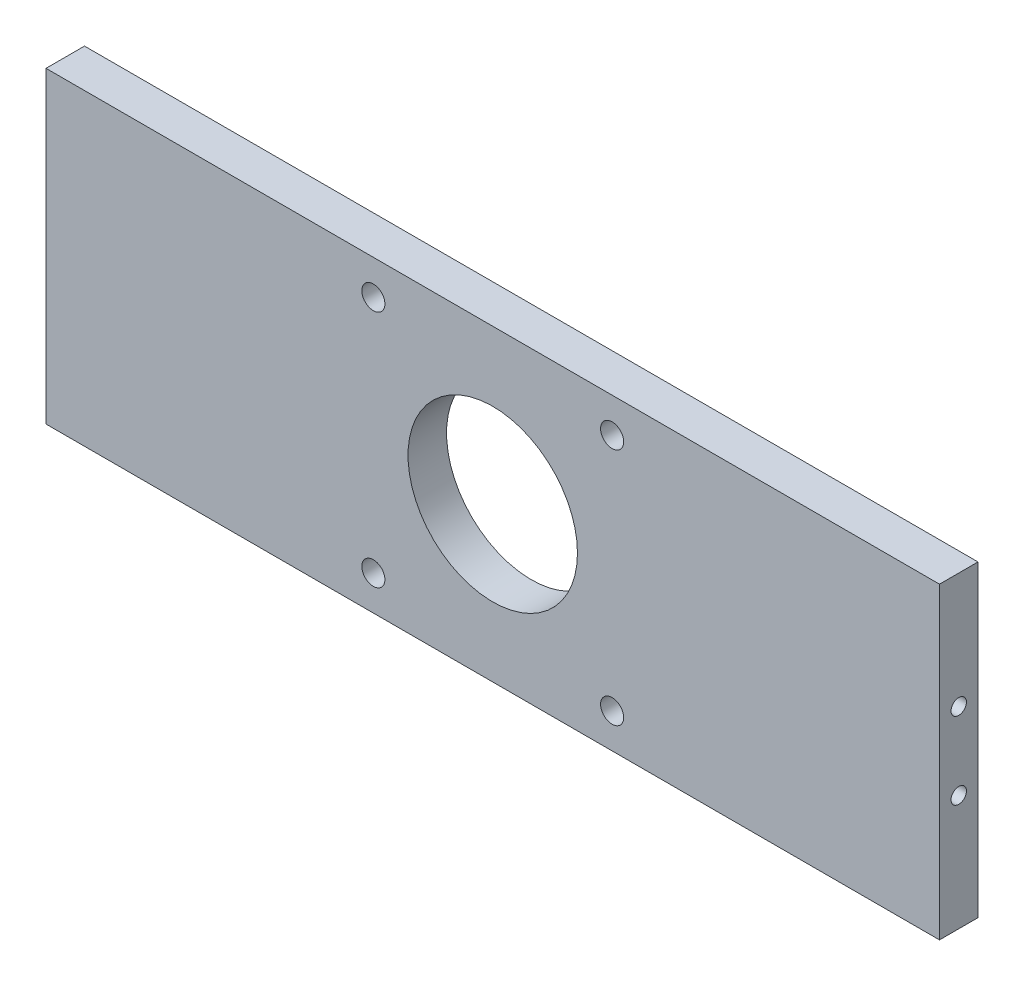
SolidWorks part; units mm, degrees
ref_plane "Front Plane" through (0, 0, 0) normal (0, 0, 1) x (1, 0, 0)
ref_plane "Top Plane" through (0, 0, 0) normal (0, 1, 0) x (1, 0, 0)
ref_plane "Right Plane" through (0, 0, 0) normal (1, 0, 0) x (0, 0, -1)
sketch "Sketch1" plane through (0, 0, 0) normal (0, 0, 1) x (1, 0, 0)
  line L1 (-58, 20) -> (58, 20)
  line L2 (-58, 20) -> (-58, -20)
  line L3 (-58, -20) -> (58, -20)
  line L4 (58, 20) -> (58, -20)
  line L5 (-58, 20) -> (58, -20) construction
  line L6 (-58, -20) -> (58, 20) construction
  line L7 (-15.5, 15.5) -> (15.5, 15.5)
  line L8 (-15.5, 15.5) -> (-15.5, -15.5)
  line L9 (-15.5, -15.5) -> (15.5, -15.5)
  line L10 (15.5, 15.5) -> (15.5, -15.5)
  line L11 (-15.5, 15.5) -> (15.5, -15.5) construction
  line L12 (-15.5, -15.5) -> (15.5, 15.5) construction
  circle A0 centre (0, 0) radius 11
  circle A1 centre (-15.5, 15.5) radius 1.5
  circle A2 centre (-15.5, -15.5) radius 1.5
  circle A3 centre (15.5, -15.5) radius 1.5
  circle A4 centre (15.5, 15.5) radius 1.5
  point P0 (0, 0)
  dimension "D3" = 22
  dimension "D6" = 3
  dimension "D7" = 3
  dimension "D8" = 3
  dimension "D9" = 3
  dimension "D1" = 40
  dimension "D2" = 116
  dimension "D4" = 31
  dimension "D5" = 31
extrude "Boss-Extrude2" add sketch "Sketch1" along normal blind 5 contours L4 L1 L2 L3 A4 L10 A3 L9 A2 L8 A1 L7 | A4 L7 A1 L8 A2 L9 A3 L10 A0
ref_plane "Plane1" through (58, 0, 0) normal (1, 0, 0) x (0, 0, -1)
sketch "Sketch4" plane through (58, 0, 0) normal (1, 0, 0) x (0, 0, -1)
  line L0 (-5, 0) -> (0, 0)
  line L1 (-5, 20) -> (-5, -20) construction
  line L2 (0, 55) -> (0, -55) construction
  circle A0 centre (-2.5, 5) radius 1
  circle A1 centre (-2.5, -5) radius 1
  dimension "D1" = 2
  dimension "D2" = 5
  dimension "D3" = 2.5
extrude "Cut-Extrude1" cut sketch "Sketch4" against normal blind 10 contours A1 | A0
ref_plane "Plane2" through (58, 0, 0) normal (1, 0, 0) x (0, 0, -1)
ref_plane "Plane3" through (-58, 0, 0) normal (-1, 0, 0) x (0, 0, 1)
sketch "Sketch6" plane through (-58, 0, 0) normal (-1, 0, 0) x (0, 0, 1)
  line L0 (0, 0) -> (5, 0)
  line L1 (0, 20) -> (0, -20) construction
  line L2 (5, 20) -> (5, -20) construction
  circle A0 centre (2.5, 5) radius 1
  circle A1 centre (2.5, -5) radius 1
  dimension "D2" = 2
  dimension "D1" = 5
  dimension "D3" = 2.5
extrude "Cut-Extrude2" cut sketch "Sketch6" against normal blind 5 contours A0 | A1
